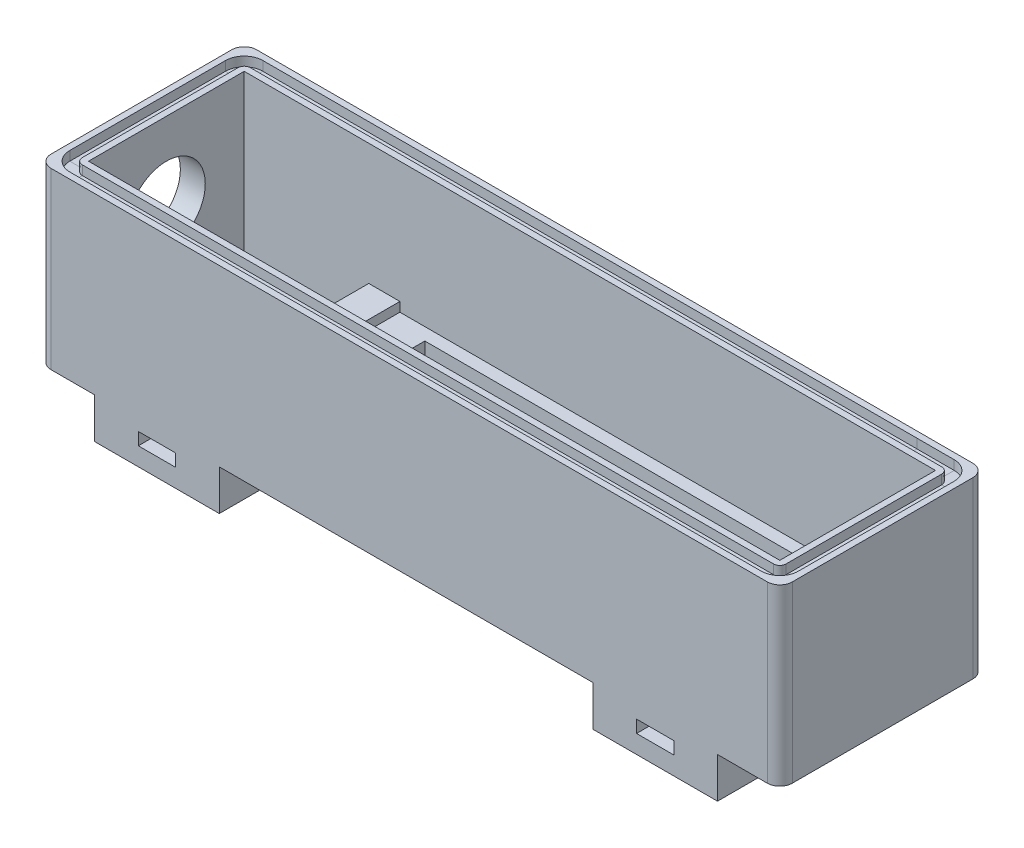
SolidWorks part; units mm, degrees
ref_plane "Płaszczyzna przednia" through (0, 0, 0) normal (0, 0, 1) x (1, 0, 0)
ref_plane "Płaszczyzna górna" through (0, 0, 0) normal (0, 1, 0) x (1, 0, 0)
ref_plane "Płaszczyzna prawa" through (0, 0, 0) normal (1, 0, 0) x (0, 0, -1)
sketch "Szkic5" plane through (0, 0, 0) normal (0, 1, 0) x (1, 0, 0)
  line L1 (-55.5, -12.5) -> (55.5, -12.5) construction
  line L2 (-55.5, -12.5) -> (-55.5, 12.5) construction
  line L3 (-55.5, 12.5) -> (55.5, 12.5) construction
  line L4 (55.5, -12.5) -> (55.5, 12.5) construction
  line L5 (-55.5, -12.5) -> (55.5, 12.5) construction
  line L6 (-55.5, 12.5) -> (55.5, -12.5) construction
  line L7 (-59.5, -16.5) -> (59.5, -16.5)
  line L8 (-59.5, -16.5) -> (-59.5, 16.5)
  line L9 (-59.5, 16.5) -> (59.5, 16.5)
  line L10 (59.5, -16.5) -> (59.5, 16.5)
  line L11 (-59.5, -16.5) -> (59.5, 16.5) construction
  line L12 (-59.5, 16.5) -> (59.5, -16.5) construction
  point P0 (0, 0)
  point P6 (0, 0)
  dimension "D1" = 25
  dimension "D2" = 111
  dimension "D3" = 4
  dimension "D4" = 4
extrude "Dodanie-wyciągnięcie3" add sketch "Szkic5" along normal blind 3
sketch "Szkic6" plane through (0, 3, 0) normal (0, 1, 0) x (1, 0, 0)
  line L1 (-55.5, -12.5) -> (55.5, -12.5)
  line L2 (-55.5, -12.5) -> (-55.5, 12.5)
  line L3 (-55.5, 12.5) -> (55.5, 12.5)
  line L4 (55.5, -12.5) -> (55.5, 12.5)
  line L5 (-55.5, -12.5) -> (55.5, 12.5) construction
  line L6 (-55.5, 12.5) -> (55.5, -12.5) construction
  line L7 (-59.5, -16.5) -> (59.5, -16.5)
  line L8 (-59.5, -16.5) -> (-59.5, 16.5)
  line L9 (-59.5, 16.5) -> (59.5, 16.5)
  line L10 (59.5, -16.5) -> (59.5, 16.5)
  line L11 (-59.5, -16.5) -> (59.5, 16.5) construction
  line L12 (-59.5, 16.5) -> (59.5, -16.5) construction
  point P0 (0, 0)
  point P6 (0, 0)
  dimension "D1" = 25
  dimension "D2" = 111
extrude "Dodanie-wyciągnięcie4" add sketch "Szkic6" along normal blind 25
sketch "Szkic7" plane through (0, 3, 0) normal (0, 1, 0) x (1, 0, 0)
  line L0 (-24.5, 10.5) -> (44.5, 10.5)
  line L4 (55.5, -12.5) -> (55.5, 12.5)
  line L5 (55.5, 12.5) -> (-35.5, 12.5)
  line L6 (55.5, 12.5) -> (-55.5, 12.5) construction
  line L7 (-24.5, -10.5) -> (44.5, -10.5)
  line L8 (0, 0) -> (0, 10.5) construction
  line L9 (0, 0) -> (0, -10.5) construction
  line L10 (44.5, 10.5) -> (44.5, -10.5)
  line L11 (-24.5, 10.5) -> (-24.5, -10.5)
  line L12 (-35.5, 12.5) -> (-35.5, -12.5)
  line L13 (-55.5, -12.5) -> (55.5, -12.5) construction
  line L14 (-35.5, -12.5) -> (55.5, -12.5)
  point P0 (0, 0)
  dimension "D1" = 21
  dimension "D2" = 69
  dimension "D3" = 11
  dimension "D4" = 11
extrude "Dodanie-wyciągnięcie5" add sketch "Szkic7" along normal blind 4
sketch "Szkic8" plane through (0, 7, 0) normal (0, 1, 0) x (1, 0, 0)
  line L0 (-55.5, -12.5) -> (55.5, -12.5) construction
  line L1 (-35.5, 12.5) -> (-30.5, 12.5)
  line L2 (-35.5, 12.5) -> (-35.5, -12.5)
  line L3 (-35.5, -12.5) -> (-30.5, -12.5)
  line L4 (-30.5, 12.5) -> (-30.5, -12.5)
  line L5 (44.5, -10.5) -> (44.5, 10.5) construction
  line L6 (55.5, 12.5) -> (48.5, 12.5)
  line L7 (55.5, 12.5) -> (55.5, -12.5)
  line L8 (55.5, -12.5) -> (48.5, -12.5)
  line L9 (48.5, 12.5) -> (48.5, -12.5)
  dimension "D1" = 79
  dimension "D2" = 4
extrude "Dodanie-wyciągnięcie6" add sketch "Szkic8" along normal blind 1.5
sketch "Szkic10" plane through (-55.5, 0, 0) normal (1, 0, 0) x (0, 0, -1)
  line L0 (12.5, 28) -> (-12.5, 3) construction
  line L1 (-12.5, 28) -> (12.5, 3) construction
  line L2 (12.5, 3) -> (-12.5, 3) construction
  circle A0 centre (0, 15.5) radius 6.25
  dimension "D1" = 12.5
extrude "Wytnij-wyciągnięcie1" cut sketch "Szkic10" against normal blind 7.5
sketch "Szkic21" plane through (0, 28, 0) normal (0, 1, 0) x (1, 0, 0)
  line L0 (55.5, 12.5) -> (-55.5, 12.5) construction
  line L1 (-55.5, 14.5) -> (55.5, 14.5)
  line L2 (-57.5, 12.5) -> (-57.5, -12.5)
  line L3 (-55.5, -14.5) -> (55.5, -14.5)
  line L4 (57.5, 12.5) -> (57.5, -12.5)
  line L5 (0, 14.5) -> (0, 12.5) construction
  line L6 (-55.5, 0) -> (-57.5, 0) construction
  line L7 (-55.5, 12.5) -> (-55.5, -12.5) construction
  line L8 (13.8887, 14.5) -> (13.8887, 16.5)
  line L9 (59.5, 16.5) -> (-59.5, 16.5) construction
  line L10 (-57.5, 2.2345) -> (-59.5, 2.2345) construction
  line L11 (-59.5, 16.5) -> (-59.5, -16.5) construction
  arc A0 (55.5, -14.5) -> (57.5, -12.5) centre (55.5, -12.5) ccw
  arc A1 (55.5, 14.5) -> (57.5, 12.5) centre (55.5, 12.5) cw
  arc A2 (-57.5, -12.5) -> (-55.5, -14.5) centre (-55.5, -12.5) ccw
  arc A3 (-55.5, 14.5) -> (-57.5, 12.5) centre (-55.5, 12.5) ccw
  dimension "D1" = 2
ref_plane "Płaszczyzna2" through (49.5, 0, 0) normal (1, 0, 0) x (0, 0, -1)
sketch "Szkic22" plane through (49.5, 0, 0) normal (1, 0, 0) x (0, 0, -1)
  line L1 (13.5, 29.5) -> (15.5, 29.5)
  line L2 (13.5, 29.5) -> (13.5, 26.5)
  line L3 (13.5, 26.5) -> (15.5, 26.5)
  line L4 (15.5, 29.5) -> (15.5, 26.5)
  line L5 (13.5, 29.5) -> (15.5, 26.5) construction
  line L6 (13.5, 26.5) -> (15.5, 29.5) construction
  line L7 (12.5, 28) -> (-12.5, 28) construction
  point P0 (14.5, 28)
  dimension "D1" = 3
  dimension "D2" = 2
sweep "Wycięcie-wyciągnięcie po ścieżce1" cut profiles "Szkic22" path "Szkic21"
sketch "Sketch1" plane through (49.5, 0, 0) normal (1, 0, 0) x (0, 0, -1)
  line L0 (-16.5, 0) -> (16.5, 0) construction
  line L1 (-16.5, 0) -> (16.5, 0)
  line L9 (16.5, 0) -> (16.5, -9)
  line L10 (16.5, -9) -> (17.8304, -12)
  line L11 (17.8304, -12) -> (18, -18.9979)
  line L16 (0, 0) -> (0, -26.3592) construction
  line L17 (18, -18.9979) -> (12.5, -18.9979)
  line L18 (-17.8304, -12) -> (-18, -18.9979)
  line L19 (-16.5, -9) -> (-17.8304, -12)
  line L20 (-16.5, 0) -> (-16.5, -9)
  line L21 (-12.5, -18.9979) -> (-18, -18.9979)
  arc A0 (12.5, -18.9979) -> (-12.5, -18.9979) centre (0, -18.9979) ccw
  point P2 (-17.9152, -15.499)
  point P6 (17.9152, -15.499)
  point P8 (0, -18.9979)
  dimension "D6" = 12.5
  dimension "D1" = 18
  dimension "D2" = 7
  dimension "D3" = 3
  dimension "D4" = 9
  dimension "D5" = 17.8304
  dimension "D7" = 12.5
extrude "Boss-Extrude2" add sketch "Sketch1" against normal blind 20 contours L17 A0 L21 L18 L19 L20 L1 L9 L10 L11
fillet "Fillet1" radius 2 6 edges at (39.5, -18.9979, -18) (39.5, -12, -17.8304) (39.5, -9, -16.5) (39.5, -9, 16.5) (39.5, -12, 17.8304) (39.5, -18.9979, 18)
sketch "Sketch2" plane through (0, 0, 16.5) normal (0, 0, 1) x (1, 0, 0)
  line L0 (29.5, -8.5764) -> (49.5, -8.5764) construction
  line L1 (29.5, -8.5764) -> (49.5, -8.5764) construction
  line L2 (29.5, 0) -> (29.5, -8.5764) construction
  line L4 (42.5, -3.5764) -> (36.5, -3.5764)
  line L5 (42.5, -3.5764) -> (42.5, -1.5764)
  line L6 (42.5, -1.5764) -> (36.5, -1.5764)
  line L7 (36.5, -3.5764) -> (36.5, -1.5764)
  line L8 (42.5, -3.5764) -> (36.5, -1.5764) construction
  line L9 (42.5, -1.5764) -> (36.5, -3.5764) construction
  point P2 (39.5, -2.5764)
  point P6 (39.5, -2.5764)
  point P12 (39.5, -2.5764)
  dimension "D1" = 10
  dimension "D2" = 6
  dimension "D3" = 2
  dimension "D4" = 6
extrude "Cut-Extrude1" cut sketch "Sketch2" against normal up to next (33 mm away) contours L5 L6 L7 L4
ref_plane "Plane1" through (-0.5, 0, 0) normal (1, 0, 0) x (0, 0, -1)
mirror "Mirror1" about plane through (-0.5, 0, 0) normal (1, 0, 0) of "Boss-Extrude2"
mirror "Mirror4" about plane through (-0.5, 0, 0) normal (1, 0, 0) of "Cut-Extrude1"
fillet "Fillet2" radius 2 6 edges at (-40.5, -9, -16.5) (-40.5, -12, -17.8304) (-40.5, -18.9979, -18) (-40.5, -18.9979, 18) (-40.5, -12, 17.8304) (-40.5, -9, 16.5)
fillet "Fillet3" radius 2 4 edges at (-59.5, 14, -16.5) (-59.5, 14, 16.5) (59.5, 14, 16.5) (59.5, 14, -16.5)
sketch "Sketch3" plane through (-50.5, 0, 0) normal (-1, 0, 0) x (0, 0, 1)
  line L0 (0, -6.4979) -> (29.0725, -6.4979)
  line L1 (29.0725, -6.4979) -> (29.0725, -24.5478)
  line L2 (29.0725, -24.5478) -> (-22.7073, -24.5478)
  line L3 (-22.7073, -24.5478) -> (-22.7073, -6.4979)
  line L4 (-22.7073, -6.4979) -> (0, -6.4979)
  line L5 (12.5, -18.9979) -> (15.951, -18.9979) construction
  dimension "D1" = 11.1221
  dimension "D2" = 17.9504
  dimension "D3" = 40.6577
  dimension "D4" = 12.5
  dimension "D5" = 5.5498
extrude "Cut-Extrude2" cut sketch "Sketch3" against normal through all
